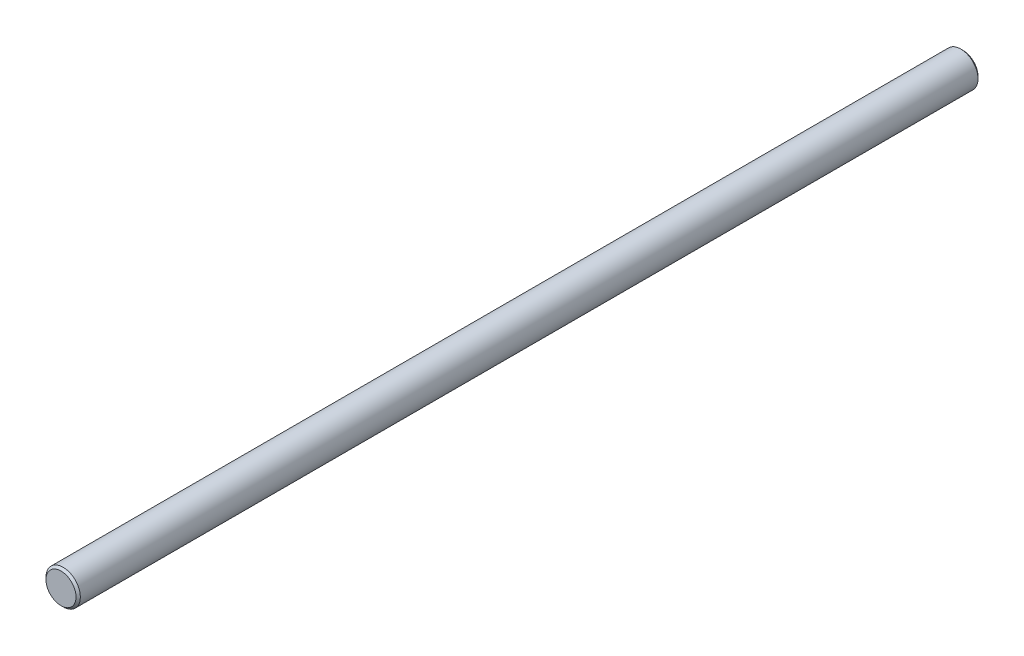
SolidWorks part; units mm, degrees
material "AISI 304"
ref_plane "Front Plane" through (0, 0, 0) normal (0, 0, 1) x (1, 0, 0)
ref_plane "Top Plane" through (0, 0, 0) normal (0, 1, 0) x (1, 0, 0)
ref_plane "Right Plane" through (0, 0, 0) normal (1, 0, 0) x (0, 0, -1)
sketch "Sketch1" plane through (0, 0, 0) normal (0, 0, 1) x (1, 0, 0)
  circle A0 centre (0, 0) radius 4
  dimension "D1" = 8
extrude "Boss-Extrude1" add sketch "Sketch1" against normal blind 210
cosmetic thread "Cosmetic Thread1" parameters "D2"=6.619
chamfer "Chamfer1" distance 0.5 angle 45 2 edges at (4, 0, -210) (4, 0, 0)
